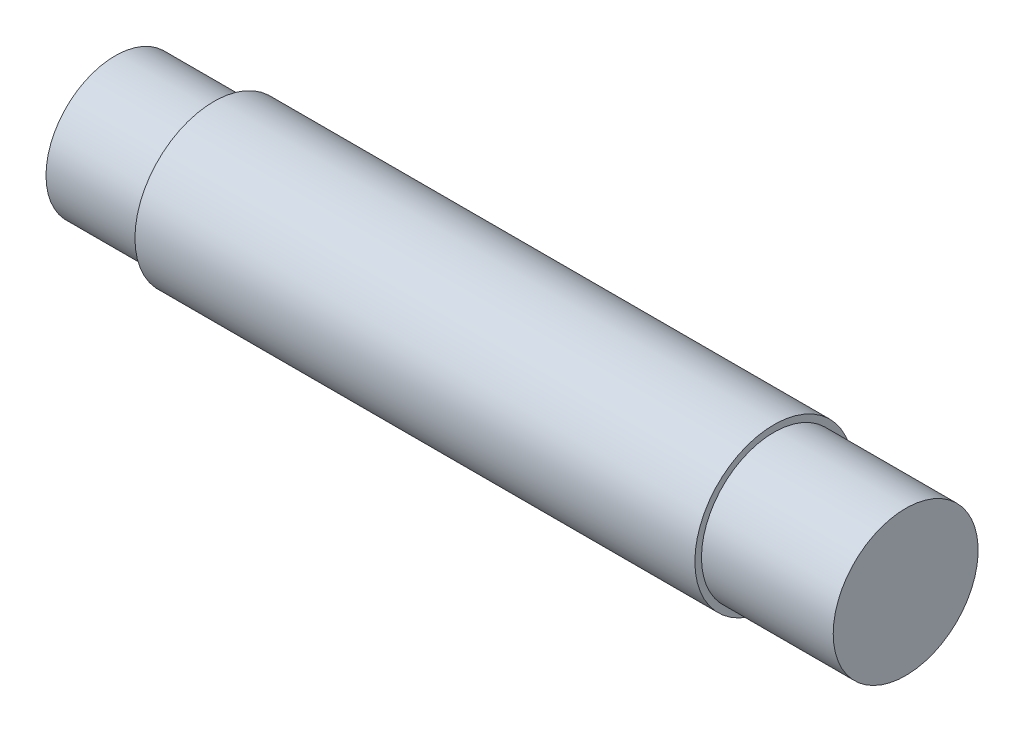
SolidWorks part; units mm, degrees
ref_plane "Front Plane" through (0, 0, 0) normal (0, 0, 1) x (1, 0, 0)
ref_plane "Top Plane" through (0, 0, 0) normal (0, 1, 0) x (1, 0, 0)
ref_plane "Right Plane" through (0, 0, 0) normal (1, 0, 0) x (0, 0, -1)
sketch "Sketch1" plane through (0, 0, 0) normal (0, 0, 1) x (1, 0, 0)
  line L0 (0, 0) -> (60, 0)
  line L1 (60, 0) -> (60, 5.5)
  line L2 (50, 6) -> (7.5, 6)
  line L3 (7.5, 6) -> (7.5, 5.25)
  line L4 (7.5, 5.25) -> (0, 5.25)
  line L5 (0, 5.25) -> (0, 0)
  line L6 (60, 5.5) -> (50, 5.5)
  line L7 (50, 5.5) -> (50, 6)
  line L8 (-6.1668, 0) -> (69.8866, 0) construction
  dimension "D1" = 60
  dimension "D2" = 50
  dimension "D3" = 11
  dimension "D4" = 12
  dimension "D5" = 10.5
  dimension "D6" = 7.5
revolve "Revolve1" add sketch "Sketch1" angle 360 about L8
